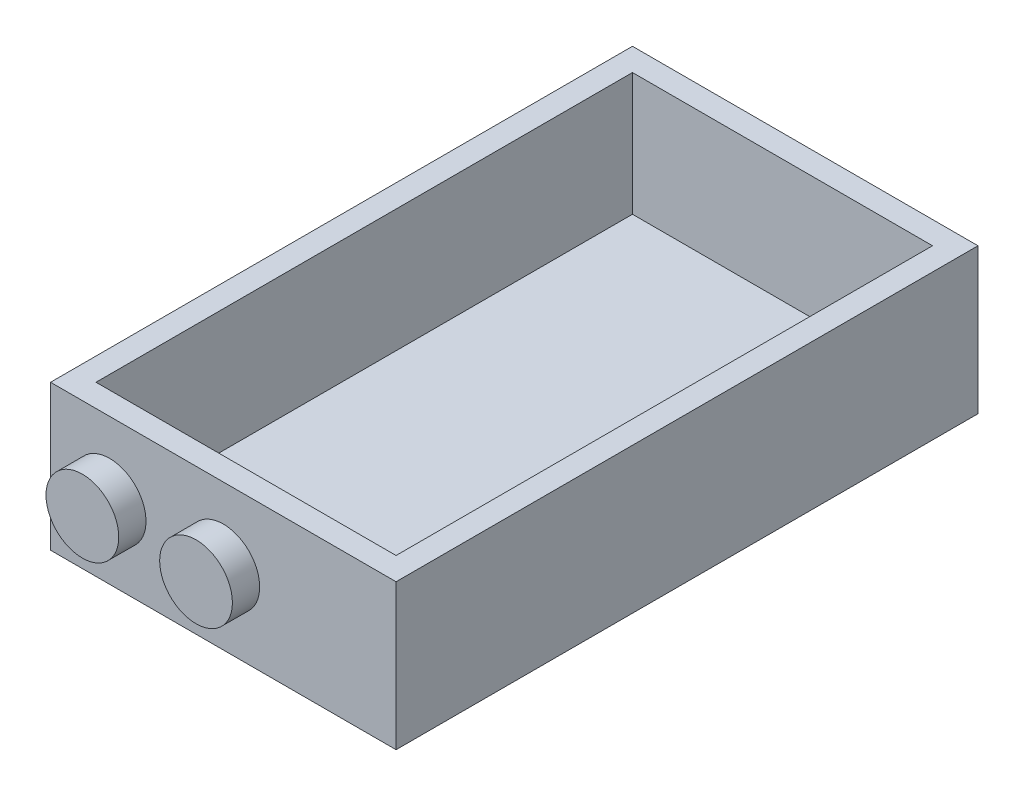
SolidWorks part; units mm, degrees
ref_plane "Front Plane" through (0, 0, 0) normal (0, 0, 1) x (1, 0, 0)
ref_plane "Top Plane" through (0, 0, 0) normal (0, 1, 0) x (1, 0, 0)
ref_plane "Right Plane" through (0, 0, 0) normal (1, 0, 0) x (0, 0, -1)
sketch "Sketch1" plane through (0, 0, 0) normal (0, 1, 0) x (1, 0, 0)
  line L1 (0, 0) -> (38, 0)
  line L2 (0, 0) -> (0, -64)
  line L3 (0, -64) -> (38, -64)
  line L4 (38, 0) -> (38, -64)
  dimension "D1" = 38
  dimension "D2" = 64
extrude "Boss-Extrude1" add sketch "Sketch1" along normal blind 16
sketch "Sketch2" plane through (0, 0, 64) normal (0, 0, 1) x (1, 0, 0)
  line L0 (0, 8) -> (38, 8) construction
  line L1 (0, 16) -> (0, 0) construction
  line L2 (38, 16) -> (38, 0) construction
  circle A0 centre (19, 8) radius 4
  circle A1 centre (6.5, 8) radius 4
  dimension "D1" = 8
  dimension "D2" = 12.5
extrude "Boss-Extrude2" add sketch "Sketch2" along normal blind 3
shell "Shell1" thickness 2.5
